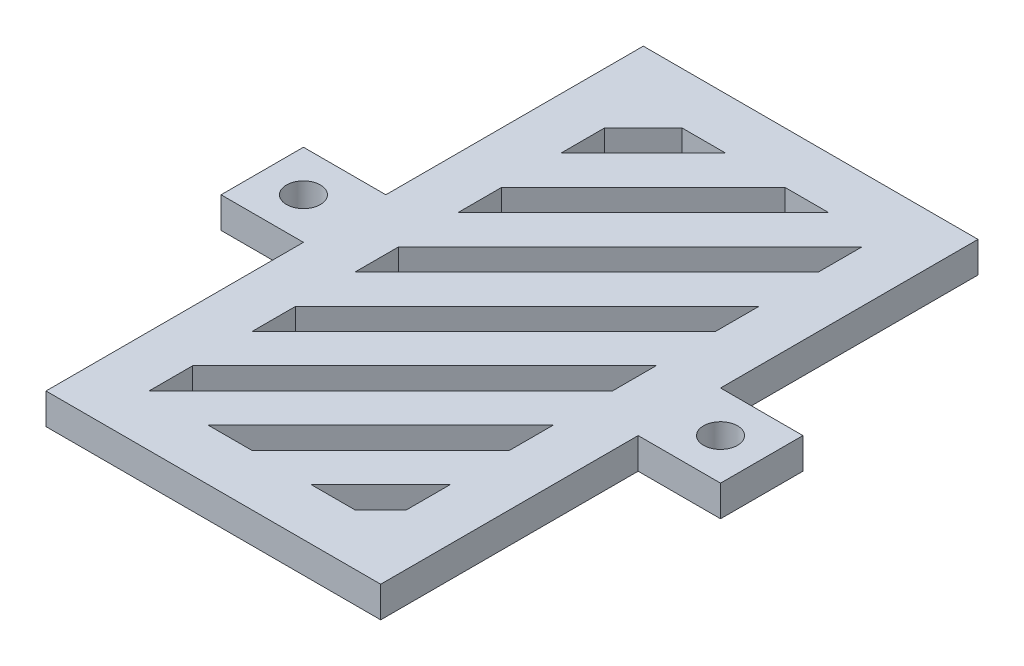
SolidWorks part; units mm, degrees
ref_plane "Front Plane" through (0, 0, 0) normal (0, 0, 1) x (1, 0, 0)
ref_plane "Top Plane" through (0, 0, 0) normal (0, 1, 0) x (1, 0, 0)
ref_plane "Right Plane" through (0, 0, 0) normal (1, 0, 0) x (0, 0, -1)
sketch "Sketch1" plane through (0, 0, 0) normal (0, 1, 0) x (1, 0, 0)
  line L0 (0, 25) -> (-8, 25)
  line L1 (0, 0) -> (32.5, 0)
  line L2 (0, 0) -> (0, 25)
  line L3 (0, 58) -> (32.5, 58)
  line L4 (32.5, 0) -> (32.5, 25)
  line L5 (-8, 25) -> (-8, 33)
  line L6 (-8, 33) -> (0, 33)
  line L7 (32.5, 25) -> (40.5, 25)
  line L8 (40.5, 25) -> (40.5, 33)
  line L9 (40.5, 33) -> (32.5, 33)
  line L10 (0, 33) -> (0, 58)
  line L11 (32.5, 33) -> (32.5, 58)
  circle A0 centre (-4, 29) radius 1.65
  circle A1 centre (36.5, 29) radius 1.65
  point P14 (-8, 29)
  point P16 (40.5, 29)
  point P19 (0, 0)
  point P20 (-4, 25)
  point P21 (0, 0)
  point P22 (0, 0)
  point P23 (36.5, 25)
  dimension "D5" = 3.3
  dimension "D1" = 32.5
  dimension "D2" = 58
  dimension "D3" = 8
  dimension "D4" = 8
extrude "Boss-Extrude1" add sketch "Sketch1" along normal blind 3
sketch "Sketch3" plane through (0, 3, 0) normal (0, 1, 0) x (1, 0, 0)
  line L0 (0, 0) -> (32.5, 0) construction
  line L1 (10.7574, 5) -> (15, 5)
  line L2 (5, 5) -> (5, 9.2426)
  line L3 (8.7574, 53) -> (13, 53)
  line L4 (27.5, 27.5) -> (27.5, 31.7426)
  line L5 (0, 25) -> (0, 0) construction
  line L6 (32.5, 0) -> (32.5, 25) construction
  line L7 (32.5, 58) -> (0, 58) construction
  line L8 (5, 5) -> (27.5, 27.5)
  line L9 (5, 9.2426) -> (27.5, 31.7426)
  line L10 (5, 15) -> (27.5, 37.5)
  line L11 (27.5, 37.5) -> (27.5, 41.7426)
  line L12 (5, 19.2426) -> (27.5, 41.7426)
  line L13 (5, 15) -> (5, 19.2426)
  line L14 (5, 25) -> (27.5, 47.5)
  line L15 (27.5, 47.5) -> (27.5, 51.7426)
  line L16 (5, 29.2426) -> (27.5, 51.7426)
  line L17 (5, 25) -> (5, 29.2426)
  line L18 (5, 35) -> (23, 53)
  line L20 (5, 39.2426) -> (18.7574, 53)
  line L21 (5, 35) -> (5, 39.2426)
  line L22 (5, 45) -> (13, 53)
  line L24 (5, 49.2426) -> (8.7574, 53)
  line L25 (5, 45) -> (5, 49.2426)
  line L26 (15, 5) -> (27.5, 17.5)
  line L27 (27.5, 17.5) -> (27.5, 21.7426)
  line L28 (10.7574, 5) -> (27.5, 21.7426)
  line L30 (25, 5) -> (27.5, 7.5)
  line L31 (27.5, 7.5) -> (27.5, 11.7426)
  line L32 (20.7574, 5) -> (27.5, 11.7426)
  line L34 (5, -5) -> (5, -0.7574) [skipped]
  line L35 (5, -15) -> (5, -10.7574) [skipped]
  line L36 (27.5, 57.5) -> (27.5, 61.7426) [skipped]
  line L37 (27.5, 67.5) -> (27.5, 71.7426) [skipped]
  line L38 (18.7574, 53) -> (23, 53)
  line L39 (20.7574, 5) -> (25, 5)
  dimension "D1" = 5
  dimension "D2" = 5
  dimension "D3" = 5
  dimension "D4" = 5
  dimension "D5" = 3
  dimension "D6" = 5
  dimension "D7" = 3
extrude "Cut-Extrude1" cut sketch "Sketch3" against normal blind 3
